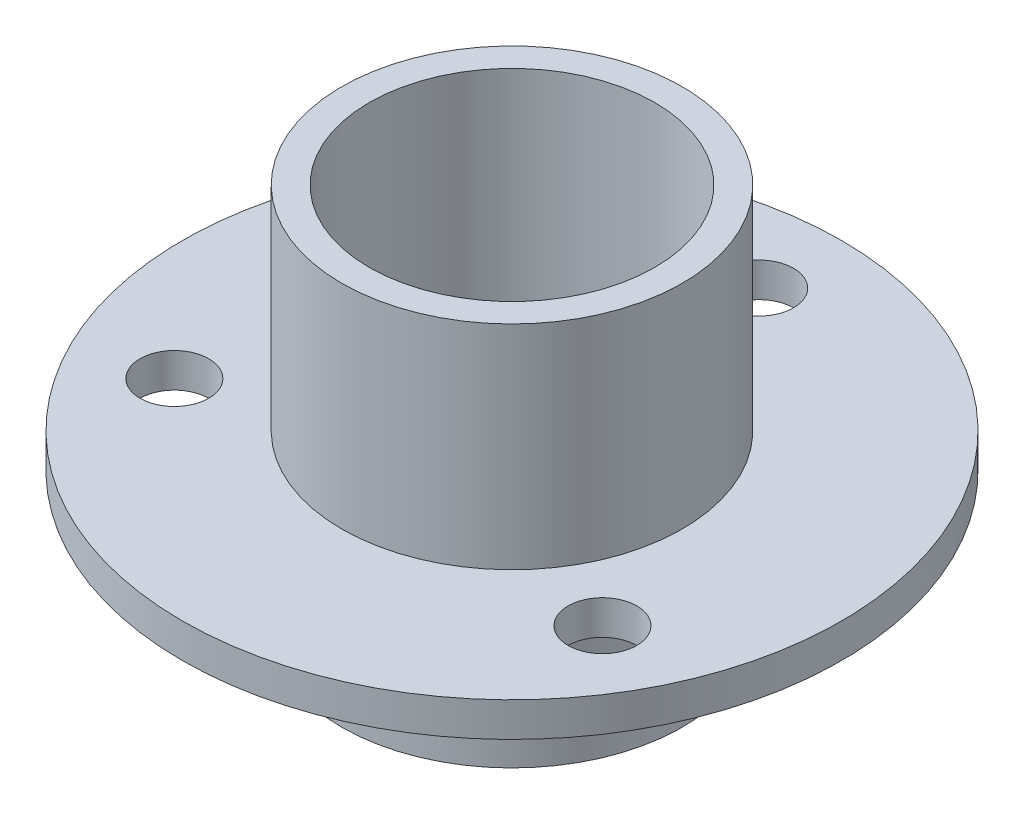
SolidWorks part; units mm, degrees
material "ABS"
ref_plane "Front Plane" through (0, 0, 0) normal (0, 0, 1) x (1, 0, 0)
ref_plane "Top Plane" through (0, 0, 0) normal (0, 1, 0) x (1, 0, 0)
ref_plane "Right Plane" through (0, 0, 0) normal (1, 0, 0) x (0, 0, -1)
sketch "Sketch1" plane through (0, 0, 0) normal (0, 1, 0) x (1, 0, 0)
  circle A0 centre (0, 0) radius 6.2
  circle A1 centre (0, 0) radius 5.2
  dimension "D1" = 12.4
  dimension "D2" = 1
extrude "Boss-Extrude1" add sketch "Sketch1" along normal blind 14
ref_plane "Plane1" through (0, 5, 0) normal (0, 1, 0) x (-1, 0, 0)
sketch "Sketch2" plane through (0, 5, 0) normal (0, 1, 0) x (-1, 0, 0)
  line L0 (0, 0) -> (0, -9) construction
  circle A0 centre (0, 0) radius 12
  circle A1 centre (0, -9) radius 1.25
  circle A2 centre (-7.7942, 4.5) radius 1.25
  circle A3 centre (7.7942, 4.5) radius 1.25
  circle A6 centre (0, 0) radius 5.2
  circle A7 centre (0, 0) radius 5.2
  dimension "D1" = 24
  dimension "D2" = 2.5
  dimension "D3" = 9
  dimension "D5" = 0
  dimension "D4" = 3
extrude "Boss-Extrude2" add sketch "Sketch2" along normal blind 1.25
